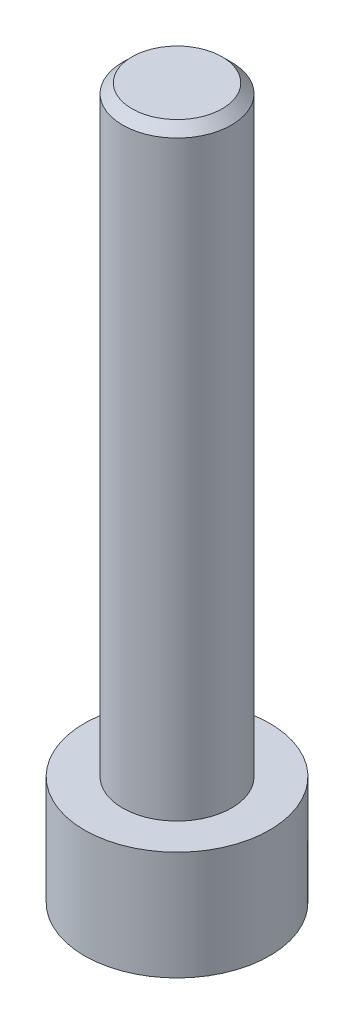
SolidWorks part; units mm, degrees
material "201 Annealed Stainless Steel (SS)"
ref_plane "Front Plane" through (0, 0, 0) normal (0, 0, 1) x (1, 0, 0)
ref_plane "Top Plane" through (0, 0, 0) normal (0, 1, 0) x (1, 0, 0)
ref_plane "Right Plane" through (0, 0, 0) normal (1, 0, 0) x (0, 0, -1)
sketch "Sketch1" plane through (0, 0, 0) normal (0, 1, 0) x (1, 0, 0)
  circle A0 centre (0, 0) radius 2.465
  dimension "D1" = 4.93
extrude "Boss-Extrude1" add sketch "Sketch1" along normal blind 2.9
sketch "Sketch2" plane through (0, 2.9, 0) normal (0, 1, 0) x (1, 0, 0)
  circle A0 centre (0, 0) radius 1.45
  dimension "D1" = 2.9
extrude "Boss-Extrude2" add sketch "Sketch2" along normal blind 16
sketch "Sketch3" plane through (0, 0, 0) normal (0, -1, 0) x (1, 0, 0)
  line L1 (0.7332, -1.27) -> (1.4665, 0)
  line L2 (1.4665, 0) -> (0.7332, 1.27)
  line L3 (0.7332, 1.27) -> (-0.7332, 1.27)
  line L4 (-0.7332, 1.27) -> (-1.4665, 0)
  line L5 (-1.4665, 0) -> (-0.7332, -1.27)
  line L6 (-0.7332, -1.27) -> (0.7332, -1.27)
  circle A0 centre (0, 0) radius 1.27 construction
  dimension "D1" = 2.54
extrude "Cut-Extrude1" cut sketch "Sketch3" against normal blind 1.9
chamfer "Chamfer1" distance 0.25 angle 45 1 edges at (0, 18.9, 1.45)
